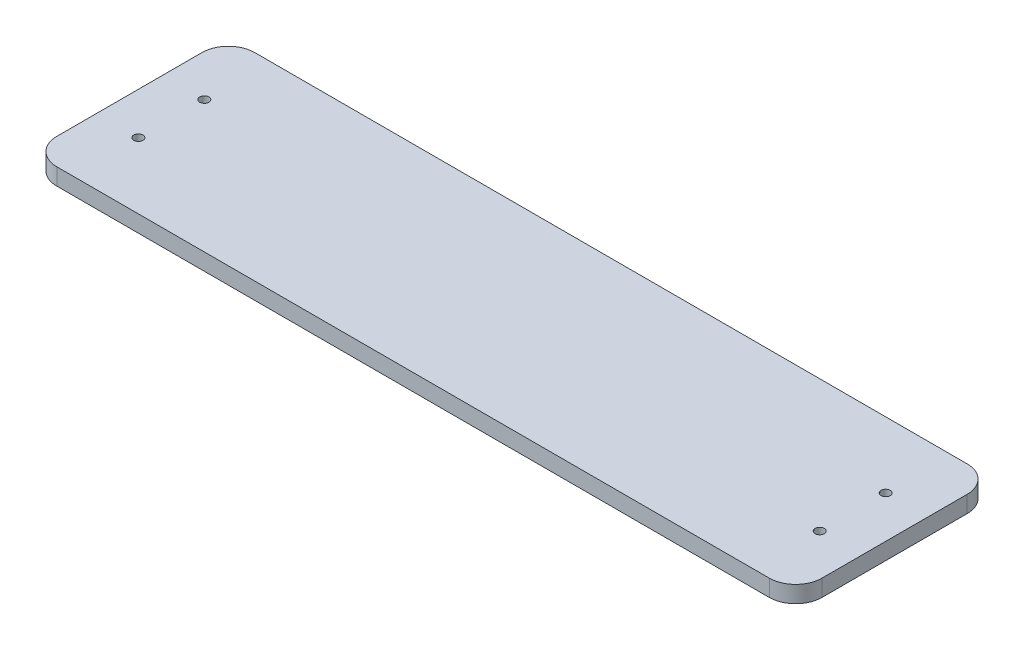
SolidWorks part; units mm, degrees
ref_plane "Front Plane" through (0, 0, 0) normal (0, 0, 1) x (1, 0, 0)
ref_plane "Top Plane" through (0, 0, 0) normal (0, 1, 0) x (1, 0, 0)
ref_plane "Right Plane" through (0, 0, 0) normal (1, 0, 0) x (0, 0, -1)
sketch "Sketch1" plane through (0, 0, 0) normal (0, 1, 0) x (1, 0, 0)
  line L1 (-145, 37.5) -> (145, 37.5)
  line L2 (-145, 37.5) -> (-145, -37.5)
  line L3 (-145, -37.5) -> (145, -37.5)
  line L4 (145, 37.5) -> (145, -37.5)
  line L5 (-145, 37.5) -> (145, -37.5) construction
  line L6 (-145, -37.5) -> (145, 37.5) construction
  point P0 (0, 0)
  dimension "D1" = 290
  dimension "D2" = 75
extrude "Boss-Extrude1" add sketch "Sketch1" along normal blind 6.35
sketch "Sketch3" plane through (0, 6.35, 0) normal (0, 1, 0) x (1, 0, 0)
  line L1 (145, 37.5) -> (-145, 37.5) construction
  circle A0 centre (129.12, 12.5) radius 1.75
  dimension "D1" = 129.12
  dimension "D3" = 3.5
  dimension "D2" = 25
extrude "Cut-Extrude2" cut sketch "Sketch3" against normal through all
fillet "Fillet1" radius 10 4 edges at (145, 3.175, -37.5) (145, 3.175, 37.5) (-145, 3.175, 37.5) (-145, 3.175, -37.5)
sketch "Sketch4" plane through (0, 6.35, 0) normal (0, 1, 0) x (1, 0, 0)
  line L0 (-145, 27.5) -> (-145, -27.5) construction
  line L1 (135, 37.5) -> (-135, 37.5) construction
  circle A0 centre (-129.12, 12.5) radius 1.75
  dimension "D1" = 3.5
  dimension "D2" = 129.12
  dimension "D3" = 15.88
  dimension "D4" = 25
extrude "Cut-Extrude3" cut sketch "Sketch4" against normal through all
pattern_linear "LPattern1" count 2 spacing 25 along (0, 0, 1) of "Cut-Extrude3", "Cut-Extrude2"
